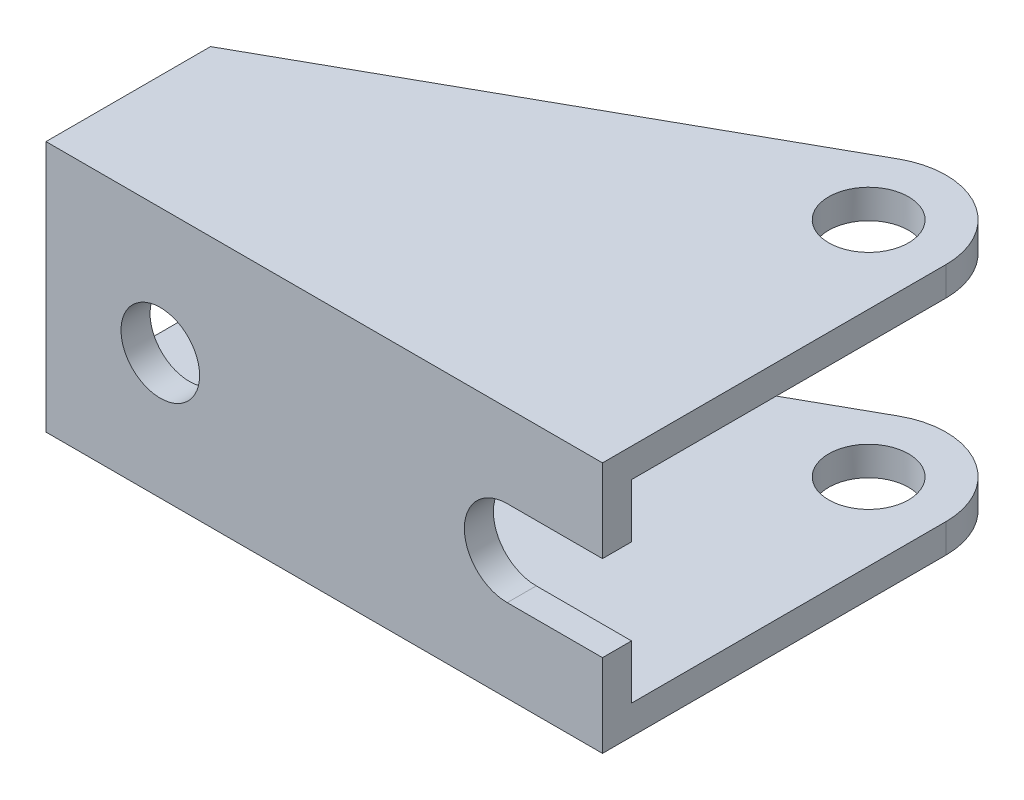
SolidWorks part; units mm, degrees
ref_plane "Front Plane" through (0, 0, 0) normal (0, 0, 1) x (1, 0, 0)
ref_plane "Top Plane" through (0, 0, 0) normal (0, 1, 0) x (1, 0, 0)
ref_plane "Right Plane" through (0, 0, 0) normal (1, 0, 0) x (0, 0, -1)
sketch "Sketch1" plane through (0, 0, 0) normal (0, 1, 0) x (1, 0, 0)
  line L0 (0, 0) -> (-58.42, 0)
  line L1 (-58.42, 0) -> (-58.42, 17.272)
  line L2 (0, 36.068) -> (0, 0)
  line L3 (0, 36.068) -> (-8.128, 36.068) construction
  line L4 (-8.128, 0) -> (-8.128, 37.084) construction
  line L5 (-58.42, 17.272) -> (-12.0933, 43.1631)
  line L6 (-8.128, 36.068) -> (-8.128, 44.196) construction
  circle A2 centre (-8.128, 36.068) radius 8.128
  circle A3 centre (-8.128, 36.068) radius 4.191
  dimension "D6" = 8.382
  dimension "D3" = 44.196
  dimension "D1" = 58.42
  dimension "D2" = 17.272
  dimension "D4" = 8.128
  dimension "D5" = 36.068
extrude "Boss-Extrude1" add sketch "Sketch1" against normal blind 26.416 contours A2 L5 L1 L0 L2 | A2 A3
sketch "Sketch2" plane through (0, 0, 0) normal (1, 0, 0) x (0, 0, -1)
  line L0 (0, 0) -> (0, -3.048) construction
  line L1 (0, -26.416) -> (0, 0) construction
  line L2 (0, -3.048) -> (3.048, -3.048) construction
  line L3 (0, 0) -> (44.196, 0) construction
  line L5 (3.048, -3.048) -> (3.048, -23.368)
  line L6 (44.196, 0) -> (36.068, 0) construction
  line L7 (44.196, 0) -> (44.196, -3.048) construction
  line L9 (3.048, -3.048) -> (44.196, -3.048)
  line L10 (3.048, -23.368) -> (44.196, -23.368)
  line L11 (44.196, -3.048) -> (44.196, -23.368)
  dimension "D1" = 3.048
  dimension "D2" = 3.048
  dimension "D3" = 20.32
  dimension "D4" = 44.196
extrude "Cut-Extrude1" cut sketch "Sketch2" against normal up to next contours L11 L10 L5 L9
sketch "Sketch3" plane through (0, 0, 0) normal (0, 0, 1) x (1, 0, 0)
  line L0 (0, 0) -> (0, -13.208) construction
  line L1 (0, -26.416) -> (0, 0) construction
  line L2 (-58.42, -13.208) -> (0, -13.208) construction
  line L3 (-58.42, -26.416) -> (-58.42, 0) construction
  line L5 (-58.42, 0) -> (-43.942, 0) construction
  line L6 (0, -13.208) -> (0, -8.708)
  line L7 (0, -8.708) -> (-10, -8.708)
  line L8 (0, -13.208) -> (0, -17.708)
  line L9 (0, 0) -> (-58.42, 0) construction
  line L10 (0, -17.708) -> (-10, -17.708)
  arc A1 (-10, -8.708) -> (-10, -17.708) centre (-10, -13.208) ccw
  circle A2 centre (-46.42, -13.208) radius 4.125
  dimension "D3" = 4.5
  dimension "D6" = 8.25
  dimension "D4" = 10
  dimension "D5" = 12
  dimension "D1" = 4.5
  dimension "D2" = 4.5
extrude "Cut-Extrude2" cut sketch "Sketch3" against normal up to next contours L7 A1 L10 L8 L6 | A2
